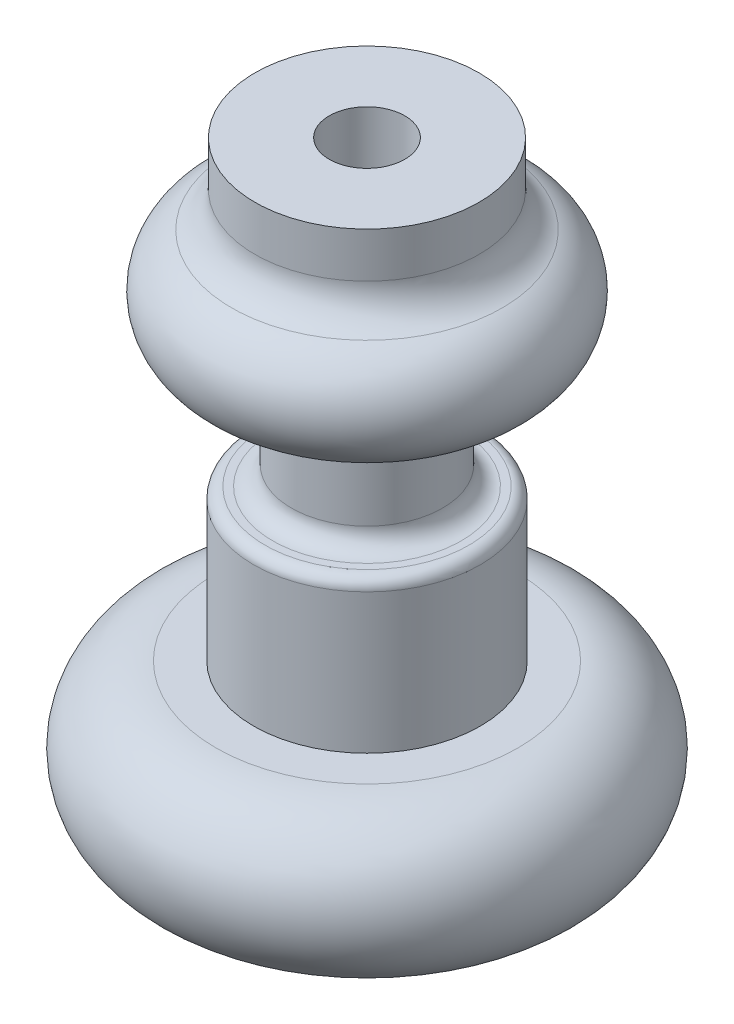
SolidWorks part; units mm, degrees
ref_plane "Front Plane" through (0, 0, 0) normal (0, 0, 1) x (1, 0, 0)
ref_plane "Top Plane" through (0, 0, 0) normal (0, 1, 0) x (1, 0, 0)
ref_plane "Right Plane" through (0, 0, 0) normal (1, 0, 0) x (0, 0, -1)
sketch "Sketch3" plane through (0, 0, 0) normal (0, 0, 1) x (1, 0, 0)
  line L0 (0, 0) -> (0, 120)
  line L1 (0, 120) -> (10, 120)
  line L2 (10, 120) -> (10, 160)
  line L3 (10, 160) -> (29.7014, 160)
  line L4 (29.7014, 160) -> (29.7014, 148.0445)
  line L5 (20, 100) -> (20, 85)
  line L6 (25, 80) -> (27.0086, 80)
  line L8 (0, 0) -> (40, 0)
  line L9 (30.0086, 77) -> (30.0086, 40)
  line L10 (30.0086, 40) -> (40, 40)
  arc A0 (29.7014, 148.0445) -> (35.8243, 138.8267) centre (39.7014, 148.0445) ccw
  arc A2 (35.8243, 138.8267) -> (30.0035, 110) centre (30.0086, 125) cw
  arc A3 (30.0035, 110) -> (20, 100) centre (30, 100) ccw
  arc A4 (20, 85) -> (25, 80) centre (25, 85) ccw
  arc A5 (27.0086, 80) -> (30.0086, 77) centre (27.0086, 77) cw
  arc A8 (40, 40) -> (40, 0) centre (40, 20) cw
  point P25 (29.13, 79.1213)
revolve "Revolve1" add sketch "Sketch3" angle 360 about L0
sketch "Sketch4" plane through (0, 0, 0) normal (0, -1, 0) x (1, 0, 0)
  text T1 "Q" font "Forte" height in points 250
extrude "Cut-Extrude1" cut sketch "Sketch4" against normal blind 10
